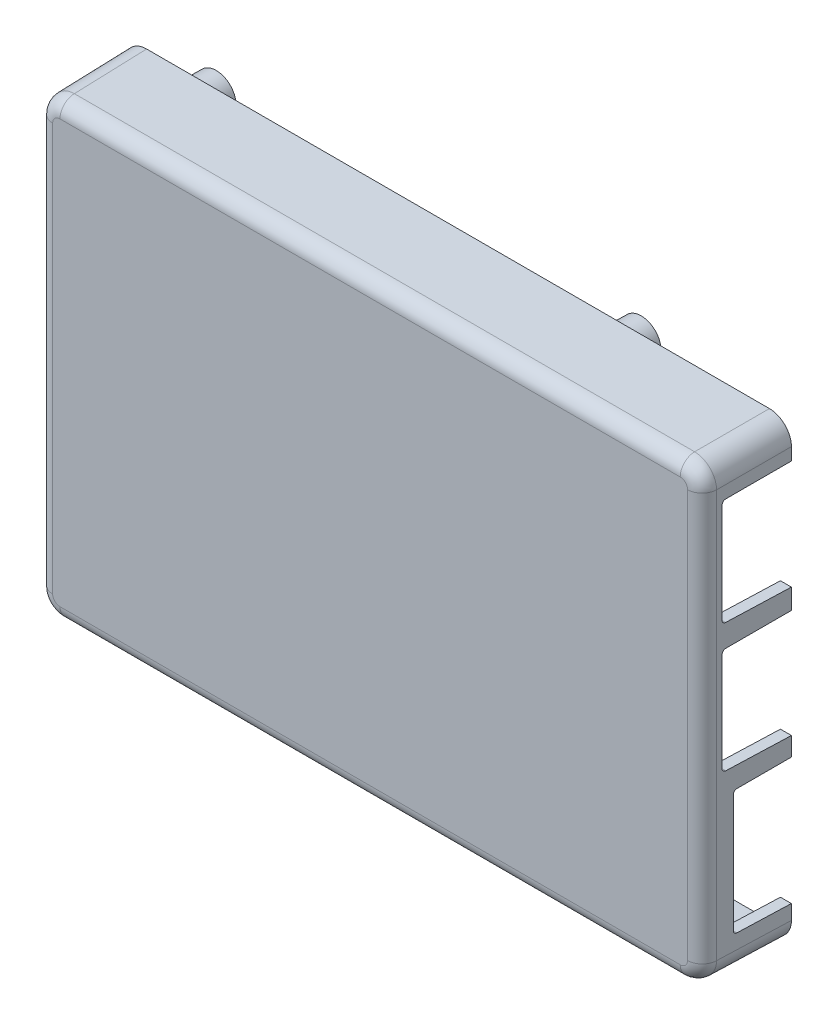
SolidWorks part; units mm, degrees
ref_plane "Front" through (0, 0, 0) normal (0, 0, 1) x (1, 0, 0)
ref_plane "Top" through (0, 0, 0) normal (0, 1, 0) x (1, 0, 0)
ref_plane "Right" through (0, 0, 0) normal (1, 0, 0) x (0, 0, -1)
sketch "Sketch1" plane through (0, 0, 0) normal (0, 0, 1) x (1, 0, 0)
  line L4 (-45.5, 31) -> (-45.5, -31)
  line L5 (-45.5, -31) -> (45.5, -31)
  line L6 (45.5, -31) -> (45.5, 31)
  line L7 (45.5, 31) -> (-45.5, 31)
  line L8 (-45.5, 31) -> (-45.5, -31)
  line L9 (-45.5, -31) -> (45.5, -31)
  line L10 (45.5, -31) -> (45.5, 31)
  line L11 (45.5, 31) -> (-45.5, 31)
  line L12 (-44, 29.5) -> (-44, -29.5)
  line L13 (-44, -29.5) -> (44, -29.5)
  line L14 (44, -29.5) -> (44, 29.5)
  line L15 (44, 29.5) -> (-44, 29.5)
  line L16 (-44, 29.5) -> (-44, -29.5)
  line L17 (-44, -29.5) -> (44, -29.5)
  line L18 (44, -29.5) -> (44, 29.5)
  line L19 (44, 29.5) -> (-44, 29.5)
  dimension "D1" = 0
  dimension "D2" = 0
extrude "Walls" add sketch "Sketch1" along normal blind 12
sketch "Sketch2" plane through (0, 0, 12) normal (0, 0, 1) x (1, 0, 0)
  line L4 (45.5, 31) -> (-45.5, 31)
  line L5 (-45.5, 31) -> (-45.5, -31)
  line L6 (-45.5, -31) -> (45.5, -31)
  line L7 (45.5, -31) -> (45.5, 31)
  line L8 (45.5, 31) -> (-45.5, 31)
  line L9 (-45.5, 31) -> (-45.5, -31)
  line L10 (-45.5, -31) -> (45.5, -31)
  line L11 (45.5, -31) -> (45.5, 31)
  dimension "D1" = 0
extrude "Top Face" add sketch "Sketch2" against normal blind 1.5
sketch "Sketch3" plane through (0, 0, 10.5) normal (0, 0, -1) x (-1, 0, 0)
  circle A0 centre (39, -24.5) radius 3
  circle A1 centre (-19, -24.5) radius 3
  circle A2 centre (39, 24.5) radius 3
  circle A3 centre (-19, 24.5) radius 3
  dimension "D1" = 6
extrude "Standoffs" add sketch "Sketch3" along normal blind 16.5 draft 1
hole_wizard "M2x0.4 Tapped Hole1" positions "Sketch5" profile "Sketch4" tap size "M2x0.4" standard "ANSI Metric"
sketch "Sketch5" plane through (0, 0, -6) normal (0, 0, -1) x (-1, 0, 0)
  point P0 (-19, -24.5)
  point P3 (-19, 24.5)
  point P6 (39, 24.5)
  point P9 (39, -24.5)
sketch "Sketch4" plane through (19, -24.5, -6) normal (1, 0, 0) x (0, 1, 0)
  line L0 (0, 0) -> (0, 5.4807)
  line L1 (0, 5.4807) -> (0.8, 5)
  line L2 (0.8, 5) -> (0.8, 0)
  line L5 (0.8, 0) -> (0, 0)
  line L10 (0, 5.4807) -> (-0.8, 5) construction
  line L11 (0, -6.35) -> (0, 107.95) construction
  dimension "Tap Drill Dia." = 1.6
  dimension "Tap Drill Depth" = 5
  dimension "Drill Angle" = 118
sketch "Sketch7" plane through (0, 0, 0) normal (1, 0, 0) x (0, 0, -1)
  line L0 (5.9, -17.348) -> (-7.3, -17.348) construction
  line L1 (5.9, -19.848) -> (5.9, -14.848) construction
  line L2 (-7.3, -25.248) -> (-7.3, -9.448) construction
  line L3 (3.0235, -9.196) -> (-7.05, -9.196) construction
  line L4 (6.4, -26) -> (-7.8, -26)
  line L5 (6.4, -26) -> (6.4, -8.696)
  line L6 (6.4, -8.696) -> (-7.8, -8.696)
  line L7 (-7.8, -26) -> (-7.8, -8.696)
  line L8 (6.4, -26) -> (-7.8, -8.696) construction
  line L9 (6.4, -8.696) -> (-7.8, -26) construction
  line L10 (-8.8, 1.25) -> (6.69, 1.25) construction
  line L11 (-8.8, 7.5) -> (-8.8, -5) construction
  line L12 (6.69, 7.74) -> (6.69, -5.24) construction
  line L13 (-8.25, 8.14) -> (6.69, 8.14) construction
  line L14 (7.19, -6.14) -> (-9.3, -6.14)
  line L15 (7.19, -6.14) -> (7.19, 8.64)
  line L16 (7.19, 8.64) -> (-9.3, 8.64)
  line L17 (-9.3, -6.14) -> (-9.3, 8.64)
  line L18 (7.19, -6.14) -> (-9.3, 8.64) construction
  line L19 (7.19, 8.64) -> (-9.3, -6.14) construction
  line L20 (-8.8, 18.85) -> (6.69, 18.85) construction
  line L21 (-8.8, 25.1) -> (-8.8, 12.6) construction
  line L22 (6.69, 25.34) -> (6.69, 12.36) construction
  line L23 (-0.1896, 25.8) -> (-3.1896, 25.8) construction
  line L24 (7.19, 11.4) -> (-9.3, 11.4)
  line L25 (7.19, 11.4) -> (7.19, 26.3)
  line L26 (7.19, 26.3) -> (-9.3, 26.3)
  line L27 (-9.3, 11.4) -> (-9.3, 26.3)
  line L28 (7.19, 11.4) -> (-9.3, 26.3) construction
  line L29 (7.19, 26.3) -> (-9.3, 11.4) construction
  point P6 (-0.7, -17.348)
  point P20 (-1.055, 1.25)
  point P34 (-1.055, 18.85)
  dimension "D1" = 0.5
  dimension "D2" = 0.5
  dimension "D3" = 0.5
  dimension "D4" = 0.5
  dimension "D5" = 0.5
extrude "USB and Ethernet Cuts" cut sketch "Sketch7" along normal through all from offset 30
draft "Draft1" type of draft neutral plane draft angle 1 faces to draft 4 face at (0, 31, 6) face at (45.5, 0.688, 4.8) face at (-45.5, 0, 6) face at (0, -31, 6) neutral plane through (0, 0, 0) neutral plane normal (0, 0, -1) reverse direction yes parameters "D1"=1
draft "Draft2" type of draft neutral plane draft angle 1 faces to draft 4 face at (0, -29.5, 5.25) face at (-44, 0, 5.25) face at (0, 29.5, 5.25) face at (44, 0.688, 4.6125) neutral plane through (0, 0, 0) neutral plane normal (0, 0, -1) parameters "D1"=1
fillet "Fillet1" radius 3 4 edges at (-45.3953, 30.8953, 6) (-45.3953, -30.8953, 6) (45.3953, 30.8953, 6) (45.3953, -30.8953, 6)
fillet "Fillet2" radius 1.5 4 edges at (-43.9084, 29.4084, 5.25) (-43.9084, -29.4084, 5.25) (43.9084, 29.4084, 5.25) (43.9084, -29.4084, 5.25)
fillet "Fillet3" radius 2 8 edges at (-44.412, -29.912, 12) (-45.2905, 0, 12) (-44.412, 29.912, 12) (0, 30.7905, 12) (44.412, 29.912, 12) (45.2905, 0, 12) (44.412, -29.912, 12) (0, -30.7905, 12)
fillet "Fillet4" radius 0.5 12 edges at (-43.3775, -28.8775, 10.5) (0, -29.3167, 10.5) (43.3775, -28.8775, 10.5) (43.8167, 0, 10.5) (43.3775, 28.8775, 10.5) (0, 29.3167, 10.5) (-43.3775, 28.8775, 10.5) (-43.8167, 0, 10.5) (-36, -24.5, 10.5) (22, -24.5, 10.5) (-36, 24.5, 10.5) (22, 24.5, 10.5)
draft "Draft3" type of draft neutral plane draft angle 1 faces to draft 6 face at (44.6819, -8.696, 3.9) face at (44.6688, 8.64, 4.65) face at (44.6688, 26.3, 4.65) face at (44.6688, 11.4, 4.65) face at (44.6688, -6.14, 4.65) face at (44.6819, -26, 3.9) neutral plane through (0, 0, 0) neutral plane normal (0, 0, -1) parameters "D1"=1
fillet "Fillet5" radius 0.5 6 edges at (44.6139, -25.8639, 7.8) (44.6139, -8.8321, 7.8) (44.5877, -5.9777, 9.3) (44.5877, 8.4777, 9.3) (44.5877, 11.5623, 9.3) (44.5877, 26.1377, 9.3)
